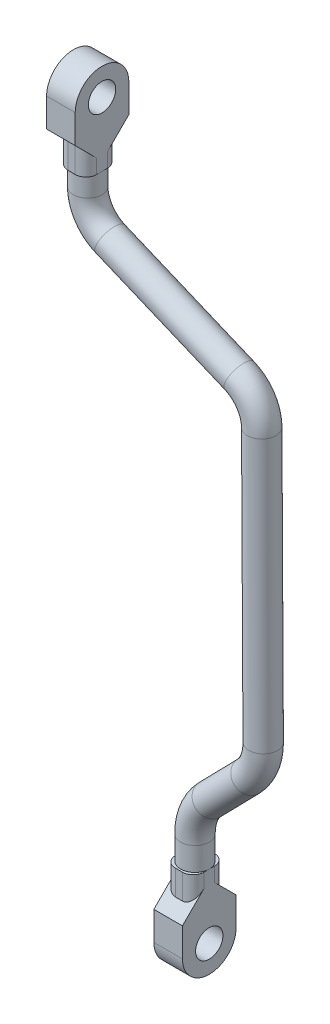
SolidWorks part; units mm, degrees
ref_plane "Front Plane" through (0, 0, 0) normal (0, 0, 1) x (1, 0, 0)
ref_plane "Top Plane" through (0, 0, 0) normal (0, 1, 0) x (1, 0, 0)
ref_plane "Right Plane" through (0, 0, 0) normal (1, 0, 0) x (0, 0, -1)
sketch "Sketch1" plane through (0, 0, 0) normal (1, 0, 0) x (0, 0, -1)
  line L0 (0, 92) -> (0, 99)
  line L1 (0, 99) -> (-3, 102)
  line L2 (-3, 102) -> (-3, 110)
  line L3 (12, 110) -> (12, 102)
  line L4 (12, 102) -> (9, 99)
  line L5 (9, 99) -> (9, 92)
  line L6 (4.5, -110) -> (4.5, 110) construction
  line L7 (0, 0) -> (72.0164, 0) construction
  line L8 (0, 92) -> (9, 92)
  arc A0 (-3, 110) -> (12, 110) centre (4.5, 110) cw
  circle A1 centre (4.5, 110) radius 3.8245
  point P15 (4.5, 92)
  dimension "D1" = 15
  dimension "D2" = 3
  dimension "D3" = 3
  dimension "D4" = 7
  dimension "D5" = 110
  dimension "D6" = 3
  dimension "D7" = 3
  dimension "D8" = 8
  dimension "D9" = 8
extrude "Boss-Extrude1" add sketch "Sketch1" along normal blind 8
fillet "Fillet1" radius 3 4 edges at (8, 95.5, -9) (0, 95.5, -9) (0, 95.5, 0) (8, 95.5, 0)
ref_plane "Plane1" through (30, 0, 0) normal (1, 0, 0) x (0, 0, -1)
sketch "Sketch4" plane through (30, 0, 0) normal (1, 0, 0) x (0, 0, -1)
  line L0 (4.5, 110) -> (4.5, -352.5159) construction
  line L9 (-0.0042, -62) -> (8.9958, -62)
  line L10 (8.9958, -69) -> (8.9958, -62)
  line L11 (11.9958, -72) -> (8.9958, -69)
  line L12 (11.9958, -80) -> (11.9958, -72)
  line L13 (-3.0042, -72) -> (-3.0042, -80)
  line L14 (-0.0042, -69) -> (-3.0042, -72)
  line L15 (-0.0042, -62) -> (-0.0042, -69)
  circle A2 centre (4.4958, -80) radius 3.8245
  arc A3 (-3.0042, -80) -> (11.9958, -80) centre (4.4958, -80) ccw
  dimension "D1" = 190
extrude "Boss-Extrude3" add sketch "Sketch4" along normal blind 8 separate body
sketch "Sketch5" plane through (0, 92, 0) normal (0, -1, 0) x (1, 0, 0)
  line L0 (8, -4.5) -> (0, -4.5) construction
  line L1 (8, -3) -> (8, -6) construction
  line L2 (0, -3) -> (0, -6) construction
  circle A0 centre (4, -4.5) radius 4
  dimension "D1" = 8
sketch3d "3DSketch1"
  line L0 (4, 92, -4.5) -> (4, 86.3521, -4.5)
  line L1 (10.4053, 77.0199, -4.3538) -> (47.3649, 62.7863, -3.5105)
  line L2 (53.7712, 53.4399, -3.4093) -> (53.6739, -23.1274, -3.9133)
  line L3 (34, -62, -4.4958) -> (34, -55.4691, -4.4958)
  line L4 (30, -62, -8.9958) -> (30, -62, 0.0042) construction
  line L5 (30, -62, -4.4958) -> (38, -62, -4.4958) construction
  line L6 (38, -62, -8.9958) -> (38, -62, 0.0042) construction
  line L7 (38.2714, -44.9843, -4.378) -> (49.4035, -33.5907, -4.071)
  arc A0 (47.3649, 62.7863, -3.5105) -> (53.7712, 53.4399, -3.4093) centre (43.7745, 53.4543, -3.6626) ccw
  arc A1 (4, 86.3521, -4.5) -> (10.4053, 77.0199, -4.3538) centre (13.9974, 86.3521, -4.2719) ccw
  arc A2 (34, -55.4691, -4.4958) -> (38.2714, -44.9843, -4.378) centre (48.9943, -55.4691, -4.0823) ccw
  arc A3 (49.4035, -33.5907, -4.071) -> (53.6739, -23.1274, -3.9133) centre (38.6771, -23.1063, -4.2261) ccw
  point P8 (53.78, 60.3157, -3.3641)
  point P9 (44.0278, 53.5198, -13.6591)
  point P12 (4, 79.4867, -4.5)
  point P13 (13.7693, 86.3521, 5.7255)
  point P20 (34, -49.356, -4.4958)
  point P22 (49.4078, -55.4691, -19.0766)
  point P27 (53.6661, -29.2279, -3.9535)
  point P28 (38.3642, -23.2046, 10.7703)
  dimension "D1" = 10
  dimension "D2" = 15
sweep "Sweep1" add profiles "Sketch5" path "3DSketch1"
fillet "Fillet3" radius 3 4 edges at (30, -65.5, 0.0042) (38, -65.5, 0.0042) (30, -65.5, -8.9958) (38, -65.5, -8.9958)
